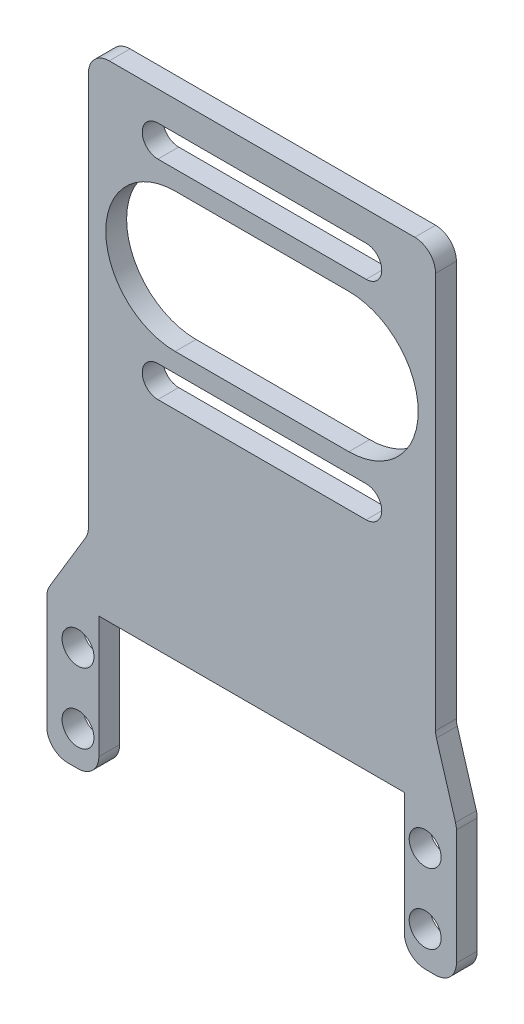
SolidWorks part; units mm, degrees
ref_plane "Front Plane" through (0, 0, 0) normal (0, 0, 1) x (1, 0, 0)
ref_plane "Top Plane" through (0, 0, 0) normal (0, 1, 0) x (1, 0, 0)
ref_plane "Right Plane" through (0, 0, 0) normal (1, 0, 0) x (0, 0, -1)
sketch "Sketch1" plane through (0, 0, 0) normal (0, 0, 1) x (1, 0, 0)
  line L0 (7.5, -20.05) -> (0, -20.05)
  line L3 (0, -20.05) -> (0, 0)
  line L4 (0, 0) -> (6, 10)
  line L5 (6, 10) -> (6, 70.5)
  line L6 (6, 70.5) -> (56, 70.5)
  line L7 (56, 70.5) -> (56, 10)
  line L8 (56, 10) -> (59, 0)
  line L9 (59, 0) -> (59, -20.05)
  line L11 (59, -20.05) -> (51.5, -20.05)
  line L12 (51.5, -20.05) -> (51.5, 0.5)
  line L14 (51.5, 0.5) -> (7.5, 0.5)
  line L15 (7.5, 0.5) -> (7.5, -20.05)
  line L17 (18.5, 49) -> (43.5, 49) construction
  line L18 (18.5, 59) -> (43.5, 59)
  line L19 (18.5, 39) -> (43.5, 39)
  line L21 (16, 64) -> (46, 64) construction
  line L22 (16, 66.25) -> (46, 66.25)
  line L23 (16, 61.75) -> (46, 61.75)
  line L24 (16, 34) -> (46, 34) construction
  line L25 (16, 36.25) -> (46, 36.25)
  line L26 (16, 31.75) -> (46, 31.75)
  arc A2 (18.5, 59) -> (18.5, 39) centre (18.5, 49) ccw
  arc A3 (43.5, 39) -> (43.5, 59) centre (43.5, 49) ccw
  circle A5 centre (4.5, -15.05) radius 2.3
  circle A6 centre (4.5, -4.95) radius 2.3
  circle A8 centre (54.5, -15.05) radius 2.3
  circle A9 centre (54.5, -4.95) radius 2.3
  arc A10 (16, 66.25) -> (16, 61.75) centre (16, 64) ccw
  arc A11 (46, 61.75) -> (46, 66.25) centre (46, 64) ccw
  arc A12 (16, 36.25) -> (16, 31.75) centre (16, 34) ccw
  arc A13 (46, 31.75) -> (46, 36.25) centre (46, 34) ccw
  point P30 (31, 49)
  point P47 (31, 64)
  point P55 (31, 34)
  dimension "D11" = 0.5
  dimension "D13" = 54.5
  dimension "D14" = 56
  dimension "D18" = 70.5
  dimension "D1" = 4.6
  dimension "D2" = 10
  dimension "D3" = 2.25
  dimension "D4" = 4.5
  dimension "D5" = 6
  dimension "D6" = 7.5
  dimension "D7" = 16
  dimension "D8" = 18.5
  dimension "D9" = 31
  dimension "D10" = 51.5
  dimension "D12" = 10
  dimension "D15" = 34
  dimension "D16" = 49
  dimension "D17" = 64
  dimension "D19" = 4.95
  dimension "D20" = 15.05
  dimension "D21" = 20.05
extrude "Boss-Extrude1" add sketch "Sketch1" along normal blind 3
fillet "Fillet1" radius 3 10 edges at (59, -20.05, 1.5) (51.5, -20.05, 1.5) (7.5, -20.05, 1.5) (0, -20.05, 1.5) (0, 0, 1.5) (6, 10, 1.5) (59, 0, 1.5) (56, 10, 1.5) (6, 70.5, 1.5) (56, 70.5, 1.5)
